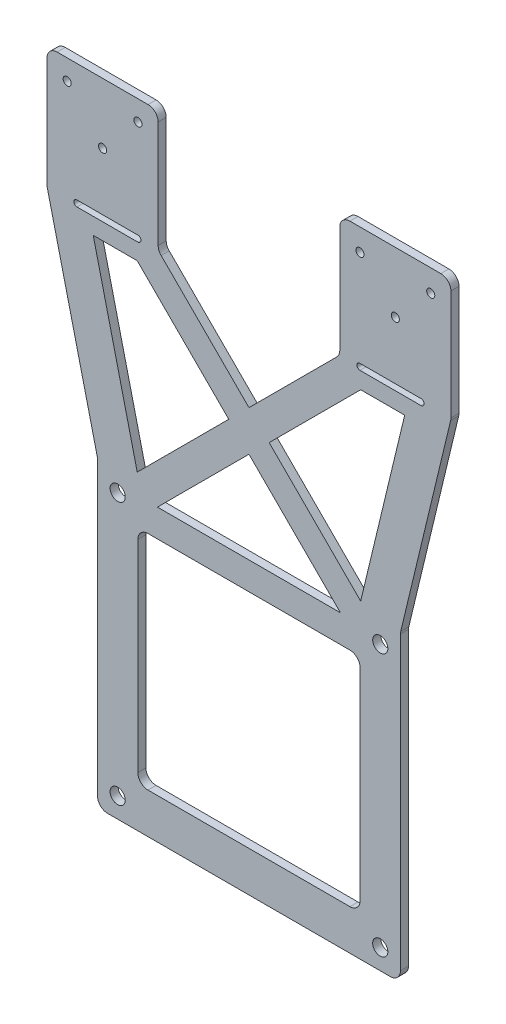
SolidWorks part; units mm, degrees
ref_plane "Front Plane" through (0, 0, 0) normal (0, 0, 1) x (1, 0, 0)
ref_plane "Top Plane" through (0, 0, 0) normal (0, 1, 0) x (1, 0, 0)
ref_plane "Right Plane" through (0, 0, 0) normal (1, 0, 0) x (0, 0, -1)
sketch "Sketch1" plane through (0, 0, 0) normal (0, 0, 1) x (1, 0, 0)
  line L1 (-37.5, -189.5484) -> (37.5, -189.5484) construction
  line L2 (-27.6564, -187.7127) -> (-38.5525, -142.3993)
  line L3 (38.5525, -142.3993) -> (27.6569, -187.7127)
  line L6 (-35, -264.5484) -> (35, -264.5484)
  line L7 (-27.5, -204.5484) -> (-27.5, -249.5484)
  line L8 (37.5, -262.0484) -> (37.5, -189.8447)
  line L9 (-37.5, -262.0484) -> (-37.5, -189.5484)
  line L10 (0, -107.5738) -> (0, -199.5484) construction
  line L11 (-16.4645, -254.5484) -> (16.4645, -254.5484)
  line L12 (27.5, -249.5484) -> (27.5, -204.5484)
  line L13 (-49.9286, -137.8619) -> (-37.5, -189.5484)
  line L14 (-22.5, -199.5484) -> (22.5, -199.5484)
  line L15 (49.9286, -137.8619) -> (37.5693, -189.2602)
  line L16 (38.5525, -142.3993) -> (27.6564, -142.3993)
  line L17 (-22.6564, -192.7127) -> (22.6569, -192.7127)
  line L18 (-42.5878, -137.5738) -> (-27.4819, -137.5738) construction
  line L19 (0, -254.5484) -> (0, -274.5996) construction
  line L20 (21.7503, -138.306) -> (0.0003, -160.056)
  line L21 (-21.7497, -138.306) -> (0.0003, -160.056)
  line L26 (-42.5878, -136.8238) -> (-27.4819, -136.8238)
  line L28 (-38.5525, -142.3993) -> (-27.6564, -142.3993)
  line L29 (-27.6564, -187.7127) -> (-4.9997, -165.056)
  line L30 (5.0003, -165.056) -> (27.6564, -142.3993)
  line L31 (-27.6564, -142.3993) -> (-4.9997, -165.056)
  line L32 (-36.2399, -107.5738) -> (-36.2399, -131.3877) construction
  line L34 (-22.5, -199.5484) -> (-25, -199.5484)
  line L36 (0.0003, -170.056) -> (22.6569, -192.7127)
  line L37 (5.0003, -165.056) -> (27.6569, -187.7127)
  line L38 (0.0003, -170.056) -> (-22.6564, -192.7127)
  line L39 (-49.9979, -137.2774) -> (-49.9979, -110.0738)
  line L40 (-42.5878, -138.3238) -> (-27.4819, -138.3238)
  line L41 (-22.4819, -136.5382) -> (-22.4819, -110.0738)
  line L42 (-27.5, -204.5484) -> (-27.5, -202.0484)
  line L43 (22.4825, -136.5382) -> (22.4825, -110.0738)
  line L44 (42.5878, -137.5738) -> (27.4819, -137.5738) construction
  line L45 (49.9979, -137.2774) -> (49.9979, -110.0738)
  line L46 (42.5878, -136.8238) -> (27.4819, -136.8238)
  line L47 (42.5878, -138.3238) -> (27.4819, -138.3238)
  line L48 (-27.5, -249.5484) -> (-27.5, -252.0484)
  line L49 (-47.4979, -107.5738) -> (-24.9819, -107.5738)
  line L50 (24.9825, -107.5738) -> (47.4979, -107.5738)
  line L51 (-16.4645, -254.5484) -> (-25, -254.5484)
  line L52 (27.5, -249.5484) -> (27.5, -252.0484)
  line L53 (16.4645, -254.5484) -> (25, -254.5484)
  line L54 (22.5, -199.5484) -> (25, -199.5484)
  line L55 (27.5, -204.5484) -> (27.5, -202.0484)
  circle A0 centre (32.5, -259.5484) radius 1.875
  circle A1 centre (-32.5, -259.5484) radius 1.875
  circle A2 centre (-32.5, -194.5484) radius 1.875
  circle A3 centre (32.5, -194.5484) radius 1.875
  arc A4 (-42.5878, -136.8238) -> (-42.5878, -138.3238) centre (-42.5878, -137.5738) ccw
  arc A5 (-27.4819, -138.3238) -> (-27.4819, -136.8238) centre (-27.4819, -137.5738) ccw
  circle A6 centre (-45, -112.5738) radius 1
  circle A7 centre (-27.4819, -112.5738) radius 1
  circle A8 centre (27.4819, -113.0294) radius 1
  circle A9 centre (45, -113.0294) radius 1
  arc A10 (42.5878, -136.8238) -> (42.5878, -138.3238) centre (42.5878, -137.5738) cw
  arc A11 (27.4819, -138.3238) -> (27.4819, -136.8238) centre (27.4819, -137.5738) cw
  circle A12 centre (-36.2399, -122.5738) radius 1
  circle A13 centre (36.2399, -122.5738) radius 1
  arc A14 (-49.9979, -110.0738) -> (-47.4979, -107.5738) centre (-47.4979, -110.0738) cw
  arc A15 (-22.4819, -110.0738) -> (-24.9819, -107.5738) centre (-24.9819, -110.0738) ccw
  arc A16 (-21.7497, -138.306) -> (-22.4819, -136.5382) centre (-19.9819, -136.5382) cw
  arc A17 (-49.9286, -137.8619) -> (-49.9979, -137.2774) centre (-47.4979, -137.2774) cw
  arc A18 (22.4825, -110.0738) -> (24.9825, -107.5738) centre (24.9825, -110.0738) cw
  arc A19 (21.7503, -138.306) -> (22.4825, -136.5382) centre (19.9825, -136.5382) ccw
  arc A21 (49.9979, -110.0738) -> (47.4979, -107.5738) centre (47.4979, -110.0738) ccw
  arc A22 (49.9286, -137.8619) -> (49.9979, -137.2774) centre (47.4979, -137.2774) ccw
  arc A23 (37.5, -189.8447) -> (37.5693, -189.2602) centre (40, -189.8447) cw
  arc A24 (35, -264.5484) -> (37.5, -262.0484) centre (35, -262.0484) ccw
  arc A25 (-35, -264.5484) -> (-37.5, -262.0484) centre (-35, -262.0484) cw
  arc A26 (25, -254.5484) -> (27.5, -252.0484) centre (25, -252.0484) ccw
  arc A27 (27.5, -202.0484) -> (25, -199.5484) centre (25, -202.0484) ccw
  arc A28 (-25, -199.5484) -> (-27.5, -202.0484) centre (-25, -202.0484) ccw
  arc A29 (-25, -254.5484) -> (-27.5, -252.0484) centre (-25, -252.0484) cw
  point P10 (0.0003, -165.5116)
  point P17 (0, -138.0294)
  point P30 (0, -227.0484)
  point P49 (-35.0349, -137.5738)
  point P60 (35.0349, -137.5738)
  point P86 (-49.9979, -137.5738)
  point P97 (49.9979, -137.5738)
  point P111 (0, -232.0484)
  dimension "D3" = 3.75
  dimension "D11" = 10
  dimension "D9" = 5
  dimension "D14" = 2.5
  dimension "D13" = 15
  dimension "D15" = 2
  dimension "D16" = 5
  dimension "D12" = 2
  dimension "D17" = 2.5
  dimension "D18" = 2.5
  dimension "D19" = 2.5
  dimension "D20" = 2.5
  dimension "D21" = 2.5
  dimension "D23" = 2.5
  dimension "D24" = 2.5
  dimension "D25" = 2.5
  dimension "D26" = 2.5
  dimension "D27" = 2.5
  dimension "D28" = 2.5
  dimension "D2" = 5
  dimension "D4" = 5
  dimension "D5" = 5
  dimension "D6" = 10
  dimension "D7" = 50
  dimension "D8" = 10
  dimension "D10" = 10
extrude "Boss-Extrude2" add sketch "Sketch1" along normal blind 2
